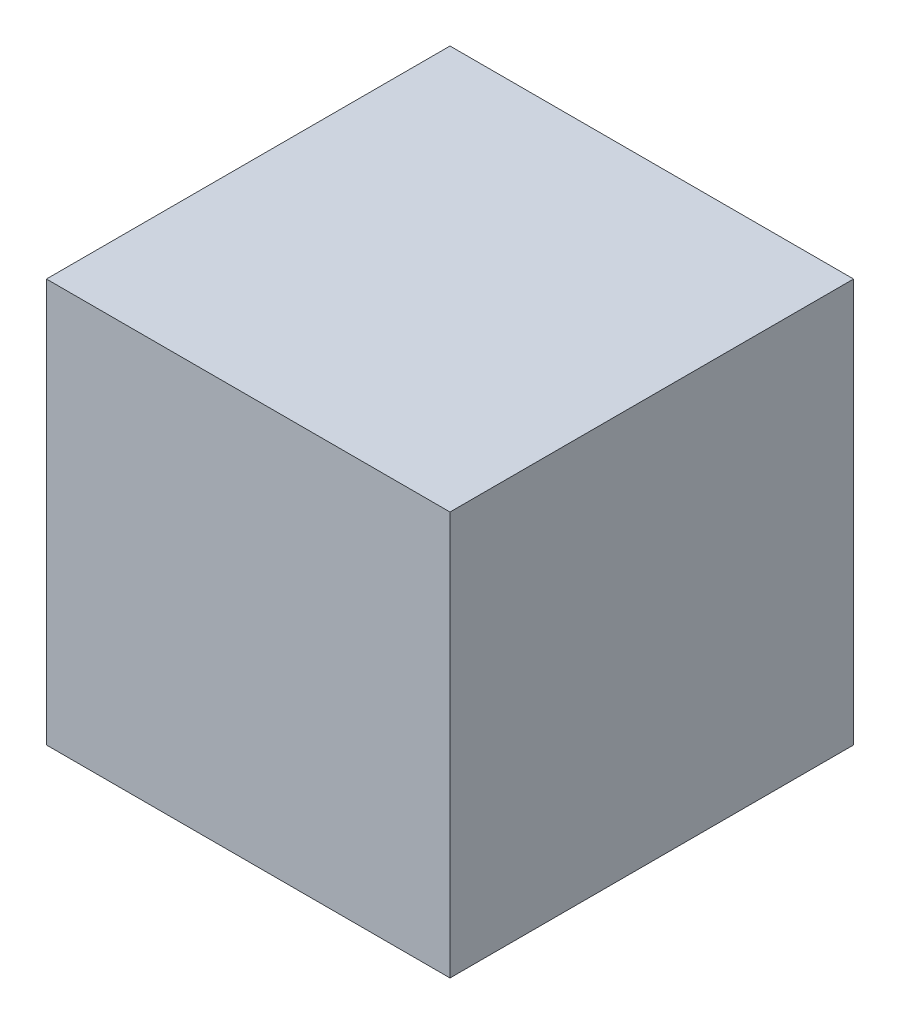
SolidWorks part; units mm, degrees
ref_plane "Front" through (0, 0, 0) normal (0, 0, 1) x (1, 0, 0)
ref_plane "Top" through (0, 0, 0) normal (0, 1, 0) x (1, 0, 0)
ref_plane "Right" through (0, 0, 0) normal (1, 0, 0) x (0, 0, -1)
sketch "Sketch1" plane through (0, 0, 0) normal (0, 1, 0) x (1, 0, 0)
  line L1 (0, 0) -> (10, 0)
  line L2 (0, 0) -> (0, 10)
  line L3 (0, 10) -> (10, 10)
  line L4 (10, 0) -> (10, 10)
  dimension "D1" = 10
extrude "Extrude1" add sketch "Sketch1" along normal blind 10
